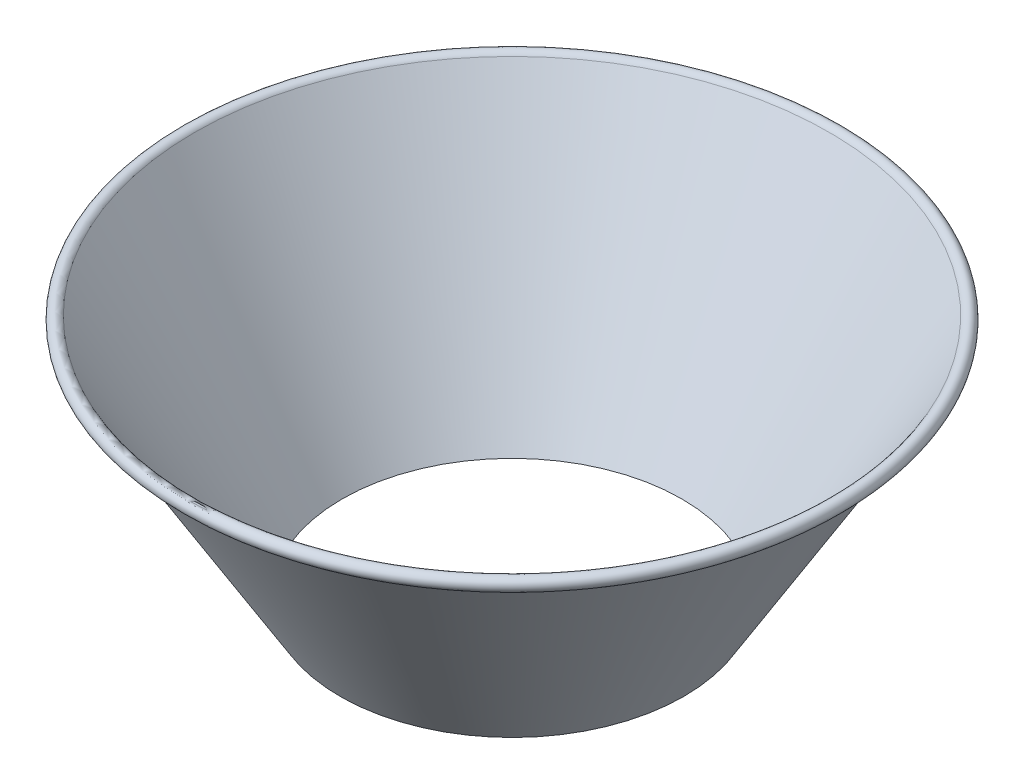
SolidWorks part; units mm, degrees
ref_plane "Front Plane" through (0, 0, 0) normal (0, 0, 1) x (1, 0, 0)
ref_plane "Top Plane" through (0, 0, 0) normal (0, 1, 0) x (1, 0, 0)
ref_plane "Right Plane" through (0, 0, 0) normal (1, 0, 0) x (0, 0, -1)
sketch "Sketch1" plane through (0, 0, 0) normal (0, 0, 1) x (1, 0, 0)
  line L0 (0, 76.2) -> (0, -76.2) construction
  line L1 (-73.025, 76.2) -> (73.025, 76.2) construction
  line L2 (-12.065, -19.05) -> (12.065, -19.05) construction
  line L3 (-6.35, -76.2) -> (6.35, -76.2) construction
  line L5 (25.4, 91.852) -> (-25.4, 91.852) construction
  line L6 (25.4, 91.852) -> (25.4, -21.9495) construction
  line L7 (25.4, -21.9495) -> (-25.4, -21.9495) construction
  line L8 (-25.4, 91.852) -> (-25.4, -21.9495) construction
  line L9 (25.4, 91.852) -> (-25.4, -21.9495) construction
  line L10 (25.4, -21.9495) -> (-25.4, 91.852) construction
  point P0 (0, 34.9513)
  point P4 (0, 0)
  point P8 (0, 76.2)
  point P11 (0, -19.05)
  point P14 (0, -76.2)
  dimension "Top OD" = 146.05
  dimension "Height" = 152.4
  dimension "Spout Length" = 57.15
  dimension "Spout OD" = 12.7
  dimension "Spout Top Diameter" = 24.13
  dimension "D1" = 50.8
sketch "Sketch3" plane through (0, 0, 0) normal (0, 0, 1) x (1, 0, 0)
  line L0 (-73.025, 74.7395) -> (-73.025, 76.2) construction
  line L1 (-73.025, 76.2) -> (73.025, 76.2) construction
  line L6 (-71.5645, 73.279) -> (-71.5645, 73.66)
  line L7 (-13.6525, -19.05) -> (13.6525, -19.05) construction
  line L9 (-12.065, -19.05) -> (-6.35, -76.2) construction
  line L10 (-6.35, -76.2) -> (-5.9671, -76.2) construction
  line L11 (-6.35, -76.2) -> (6.35, -76.2) construction
  line L12 (-5.9671, -76.2) -> (-11.6821, -19.05) construction
  line L16 (-12.065, -19.05) -> (-12.1031, -18.669)
  line L17 (-12.1031, -18.669) -> (-13.4375, -18.669)
  line L18 (-13.4375, -18.669) -> (-70.3144, 75.4946)
  line L19 (-13.6525, -19.05) -> (-70.1319, 74.4556)
  line L20 (-70.1319, 74.4556) -> (-70.6405, 75.2976)
  line L21 (-12.065, -19.05) -> (-13.6525, -19.05)
  circle A0 centre (-71.5645, 74.7395) radius 1.4605 construction
  arc A1 (-71.5645, 73.279) -> (-70.3144, 75.4946) centre (-71.5645, 74.7395) cw
  circle A3 centre (-71.5645, 74.7395) radius 1.0795 construction
  arc A4 (-71.5645, 73.66) -> (-70.6405, 75.2976) centre (-71.5645, 74.7395) cw
  point P21 (0, -19.05)
  dimension "D1" = 2.921
  dimension "D3" = 0.381
  dimension "D4" = 0.381
  dimension "D5" = 0.381
  dimension "D6" = 0.381
  dimension "D2" = 1.5875
revolve "Revolve1" add sketch "Sketch3" angle 360 about L0
sketch "Sketch4" plane through (0, 0, 0) normal (0, 0, 1) x (1, 0, 0)
  line L0 (-5.9671, -76.2) -> (-11.6821, -19.05) construction
  line L1 (-12.065, -19.05) -> (-6.35, -76.2) construction
  line L2 (-5.9671, -76.2) -> (-11.6821, -19.05)
  line L3 (-12.065, -19.05) -> (-6.35, -76.2)
  line L4 (-5.9671, -76.2) -> (-6.35, -76.2)
  line L5 (-12.065, -19.05) -> (-12.1031, -18.669)
  line L6 (-12.1031, -18.669) -> (-13.4375, -18.669)
  line L7 (-13.4375, -18.669) -> (-13.6355, -18.3412)
  line L8 (-13.4375, -18.669) -> (-70.3144, 75.4946) construction
  line L9 (-13.6355, -18.3412) -> (-11.753, -18.3412)
  line L10 (-11.753, -18.3412) -> (-11.6821, -19.05)
revolve "Revolve2" add sketch "Sketch4" angle 360 about L0
fillet "Fillet1" radius 2.54 1 edges at (-13.6525, -19.05, 0)
sketch "Sketch9" plane through (0, 0, 0) normal (0, 0, 1) x (1, 0, 0)
  line L0 (0, 0) -> (0, 76.2) construction
  line L1 (71.5645, 76.2) -> (-71.5645, 76.2) construction
  line L4 (-73.025, 76.2) -> (73.025, 76.2)
  line L5 (-6.35, -76.2) -> (6.35, -76.2)
  line L6 (12.065, -19.05) -> (-12.065, -19.05)
  point P8 (12.065, -19.05)
  point P11 (0, 76.2)
  point P14 (0, -76.2)
  point P17 (0, -19.05)
  point P18 (-73.025, 76.2)
  point P19 (-12.065, -19.05)
  point P20 (-6.35, -76.2)
  point P21 (6.35, -76.2)
  dimension "D1" = 12.7
  dimension "D2" = 24.13
  dimension "D4" = 146.05
sketch "Sketch11" plane through (0, 0, 0) normal (0, 0, 1) x (1, 0, 0)
  line L0 (-24.6831, 76.2) -> (-24.6831, 21.445) construction
  line L5 (71.5645, 76.2) -> (-71.5645, 76.2) construction
  line L6 (14.3935, -17.8232) -> (70.6405, 75.2976) construction
  line L7 (38.1123, 21.445) -> (-38.0877, 21.445)
  line L8 (38.1123, 21.445) -> (38.1123, -92.855)
  line L9 (38.1123, -92.855) -> (-38.0877, -92.855)
  line L10 (-38.0877, 21.445) -> (-38.0877, -92.855)
  line L11 (38.1123, 21.445) -> (-38.0877, -92.855) construction
  line L12 (38.1123, -92.855) -> (-38.0877, 21.445) construction
  point P0 (0.0123, -35.705)
  dimension "D1" = 76.2
  dimension "D2" = 114.3
  dimension "D3" = 54.755
extrude "Cut-Extrude1" cut sketch "Sketch11" against normal through all both and the other way through all
equation "\"D4@Sketch3\" = \"D3@Sketch3\""
equation "\"D5@Sketch3\" = \"D3@Sketch3\""
equation "\"D6@Sketch3\" = \"D3@Sketch3\""
equation "\"D1@Sketch9\" = \"Spout OD@Sketch1\""
equation "\"D2@Sketch9\" = \"Spout Top Diameter@Sketch1\""
equation "\"D4@Sketch9\" = \"Top OD@Sketch1\""
equation "\"Spout Top Diameter@Sketch1\"=\"Spout OD@Sketch1\"*1.9"
